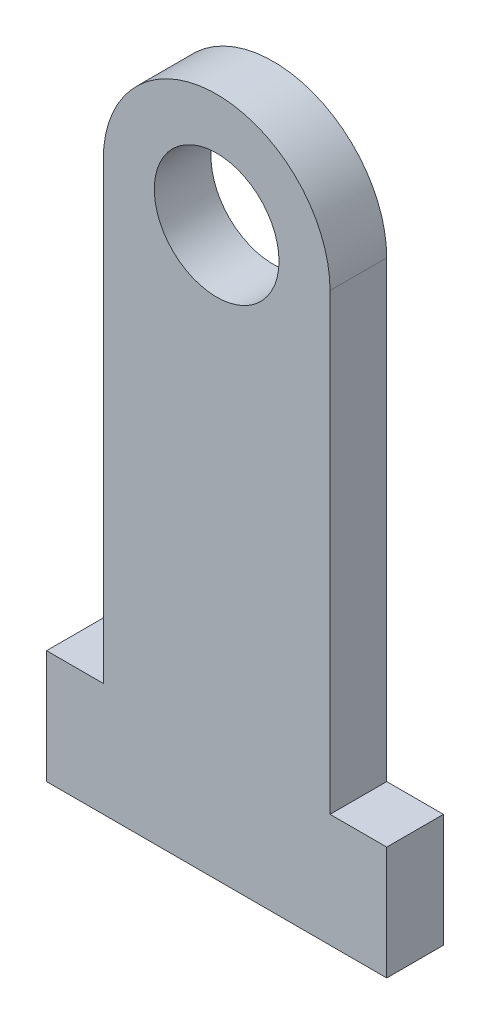
SolidWorks part; units mm, degrees
ref_plane "Front Plane" through (0, 0, 0) normal (0, 0, 1) x (1, 0, 0)
ref_plane "Top Plane" through (0, 0, 0) normal (0, 1, 0) x (1, 0, 0)
ref_plane "Right Plane" through (0, 0, 0) normal (1, 0, 0) x (0, 0, -1)
sketch "Sketch1" plane through (0, 0, 0) normal (0, 0, 1) x (1, 0, 0)
  line L0 (10, 20) -> (0, 20)
  line L1 (0, 0) -> (60, 0)
  line L2 (0, 0) -> (0, 20)
  line L3 (50, 20) -> (60, 20)
  line L4 (60, 0) -> (60, 20)
  line L6 (10, 20) -> (10, 100)
  line L8 (50, 20) -> (50, 100)
  line L9 (50, 100) -> (10, 100)
  arc A0 (50, 100) -> (10, 100) centre (30, 100) ccw
  dimension "D5" = 20
  dimension "D1" = 40
  dimension "D2" = 60
  dimension "D3" = 20
  dimension "D4" = 80
extrude "Boss-Extrude1" add sketch "Sketch1" along normal blind 10 contours L8 L9 L6 L0 L2 L1 L4 L3 | L9 A0
sketch "Sketch2" plane through (0, 0, 10) normal (0, 0, 1) x (1, 0, 0)
  circle A0 centre (30, 100) radius 11
  dimension "D1" = 22
extrude "Cut-Extrude1" cut sketch "Sketch2" against normal blind 10
ref_plane "Plane1" through (0, 0, 5) normal (0, 0, 1) x (1, 0, 0)
